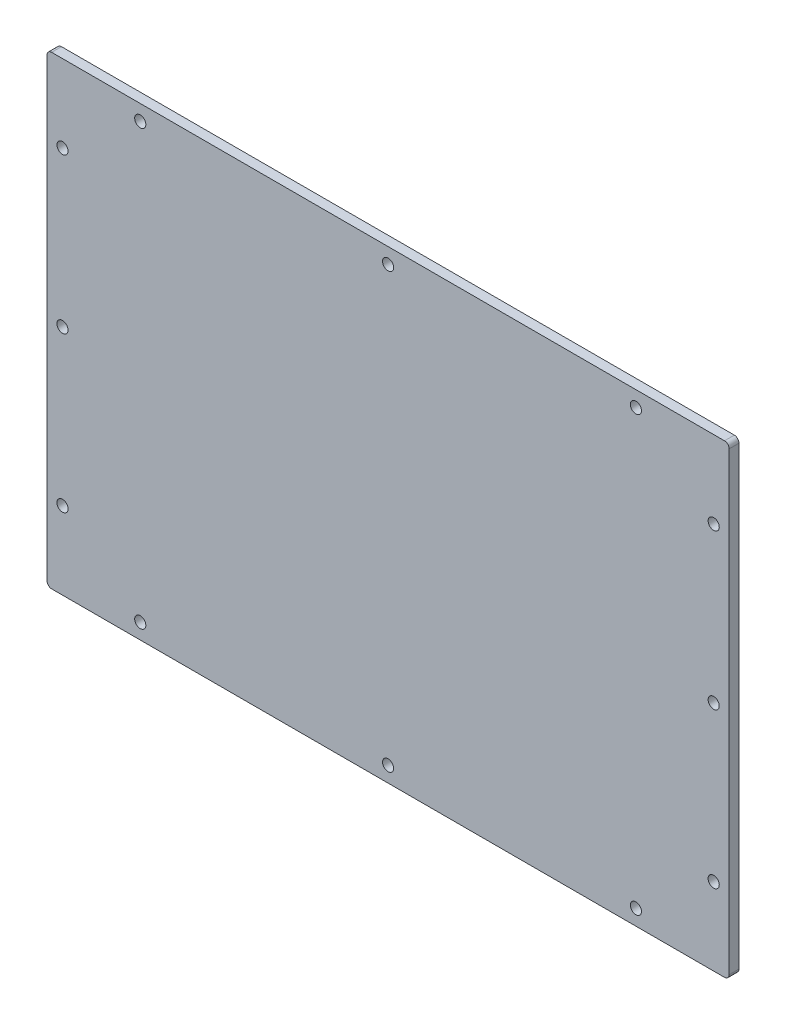
SolidWorks part; units mm, degrees
ref_plane "Front Plane" through (0, 0, 0) normal (0, 0, 1) x (1, 0, 0)
ref_plane "Top Plane" through (0, 0, 0) normal (0, 1, 0) x (1, 0, 0)
ref_plane "Right Plane" through (0, 0, 0) normal (1, 0, 0) x (0, 0, -1)
sketch "Sketch1" plane through (0, 0, 0) normal (0, 0, 1) x (1, 0, 0)
  line L0 (0, 0) -> (0, 75) construction
  line L1 (-110.105, -75) -> (110.105, -75)
  line L2 (-110.105, -75) -> (-110.105, 75)
  line L3 (-110.105, 75) -> (110.105, 75)
  line L4 (110.105, -75) -> (110.105, 75)
  line L5 (-110.105, -75) -> (110.105, 75) construction
  line L6 (-110.105, 75) -> (110.105, -75) construction
  line L15 (0, 0) -> (-110.105, 0) construction
  point P0 (0, 0)
  dimension "D1" = 220.21
  dimension "D2" = 150
extrude "Boss-Extrude1" add sketch "Sketch1" along normal blind 3.175
hole_wizard "M3 Clearance Hole1" positions "Sketch2" profile "Sketch3" hole size "M3" standard "ANSI Metric" end condition through all
sketch "Sketch2" plane through (0, 0, 3.175) normal (0, 0, 1) x (1, 0, 0)
  line L1 (-105.105, -70) -> (105.105, -70)
  line L2 (-105.105, -70) -> (-105.105, 70)
  line L3 (-105.105, 70) -> (105.105, 70)
  line L4 (105.105, -70) -> (105.105, 70)
  line L5 (-105.105, -70) -> (105.105, 70) construction
  line L6 (-105.105, 70) -> (105.105, -70) construction
  line L7 (-110.105, -75) -> (-110.105, 75) construction
  line L8 (-110.105, 75) -> (110.105, 75) construction
  point P2 (0, 0)
  point P113 (-80, 70)
  point P115 (80, 70)
  point P116 (0, 70)
  point P118 (-105.105, 50)
  point P120 (-105.105, 0)
  point P122 (-105.105, -50)
  point P124 (-80, -70)
  point P126 (0, -70)
  point P128 (80, -70)
  point P130 (105.105, -50)
  point P132 (105.105, 0)
  point P134 (105.105, 50)
  dimension "D1" = 5
  dimension "D2" = 5
  dimension "D3" = 80
  dimension "D4" = 80
  dimension "50" = 50
  dimension "D6" = 50
sketch "Sketch3" plane through (0, 0, 3.175) normal (1, 0, 0) x (0, -1, 0)
  line L0 (0, 0) -> (0, 3.175)
  line L1 (0, 3.175) -> (1.8, 3.175)
  line L2 (1.8, 3.175) -> (1.8, 0)
  line L5 (1.8, 0) -> (0, 0)
  line L11 (0, -6.35) -> (0, 107.95) construction
  dimension "Thru Hole Dia." = 3.6
  dimension "Thru Hole Depth" = 3.175
sketch "Sketch4" plane through (0, 0, 3.175) normal (0, 0, 1) x (1, 0, 0)
  line L1 (-5, -5) -> (5, -5)
  line L2 (-5, -5) -> (-5, 5)
  line L3 (-5, 5) -> (5, 5)
  line L4 (5, -5) -> (5, 5)
  line L5 (-5, -5) -> (5, 5) construction
  line L6 (-5, 5) -> (5, -5) construction
  point P0 (0, 0)
  dimension "D1" = 10
  dimension "D2" = 10
extrude "Boss-Extrude2" add sketch "Sketch4" against normal through all
fillet "Fillet2" radius 1.5 4 edges at (-110.105, -75, 1.5875) (110.105, -75, 1.5875) (110.105, 75, 1.5875) (-110.105, 75, 1.5875)
